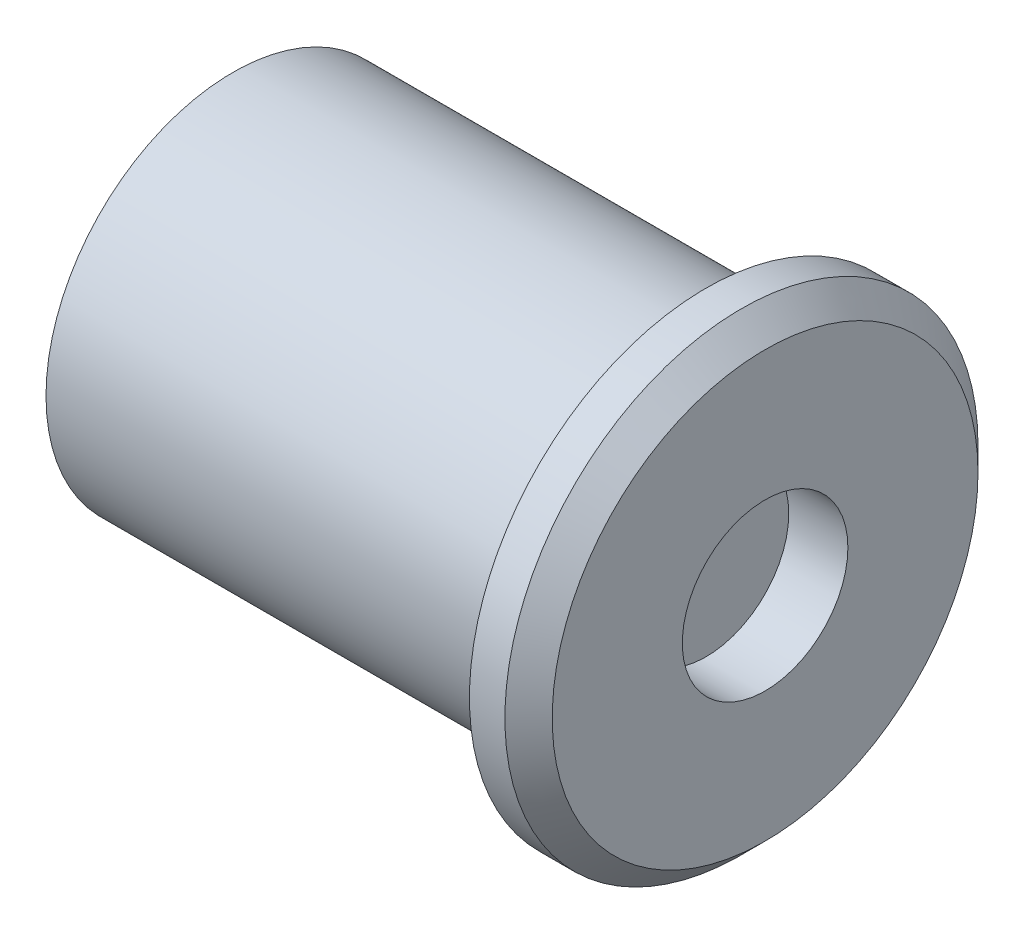
SolidWorks part; units mm, degrees
ref_plane "前视基准面" through (0, 0, 0) normal (0, 0, 1) x (1, 0, 0)
ref_plane "上视基准面" through (0, 0, 0) normal (0, 1, 0) x (1, 0, 0)
ref_plane "右视基准面" through (0, 0, 0) normal (1, 0, 0) x (0, 0, -1)
sketch "草图1" plane through (0, 0, 0) normal (1, 0, 0) x (0, 0, -1)
  circle A0 centre (0, 0) radius 7.9
extrude "凸台-拉伸1" add sketch "草图1" against normal blind 20
sketch "草图5" plane through (0, 0, 0) normal (0, 1, 0) x (1, 0, 0)
  line L0 (0, 0) -> (-10, 0) construction
  circle A0 centre (-10, 0) radius 3.1
extrude "切除-拉伸2" [suppressed] cut sketch "草图5" against normal mid plane 40 contours A0
sketch "草图6" plane through (0, 0, 0) normal (1, 0, 0) x (0, 0, -1)
  circle A0 centre (0, 0) radius 10
extrude "凸台-拉伸2" add sketch "草图6" along normal blind 2.5
sketch "草图7" plane through (2.5, 0, 0) normal (1, 0, 0) x (0, 0, -1)
  circle A0 centre (0, 0) radius 3.5
extrude "切除-拉伸3" cut sketch "草图7" against normal blind 2.5 contours A0
chamfer "倒角1" distance 1 angle 45 1 edges at (2.5, 0, -10)
